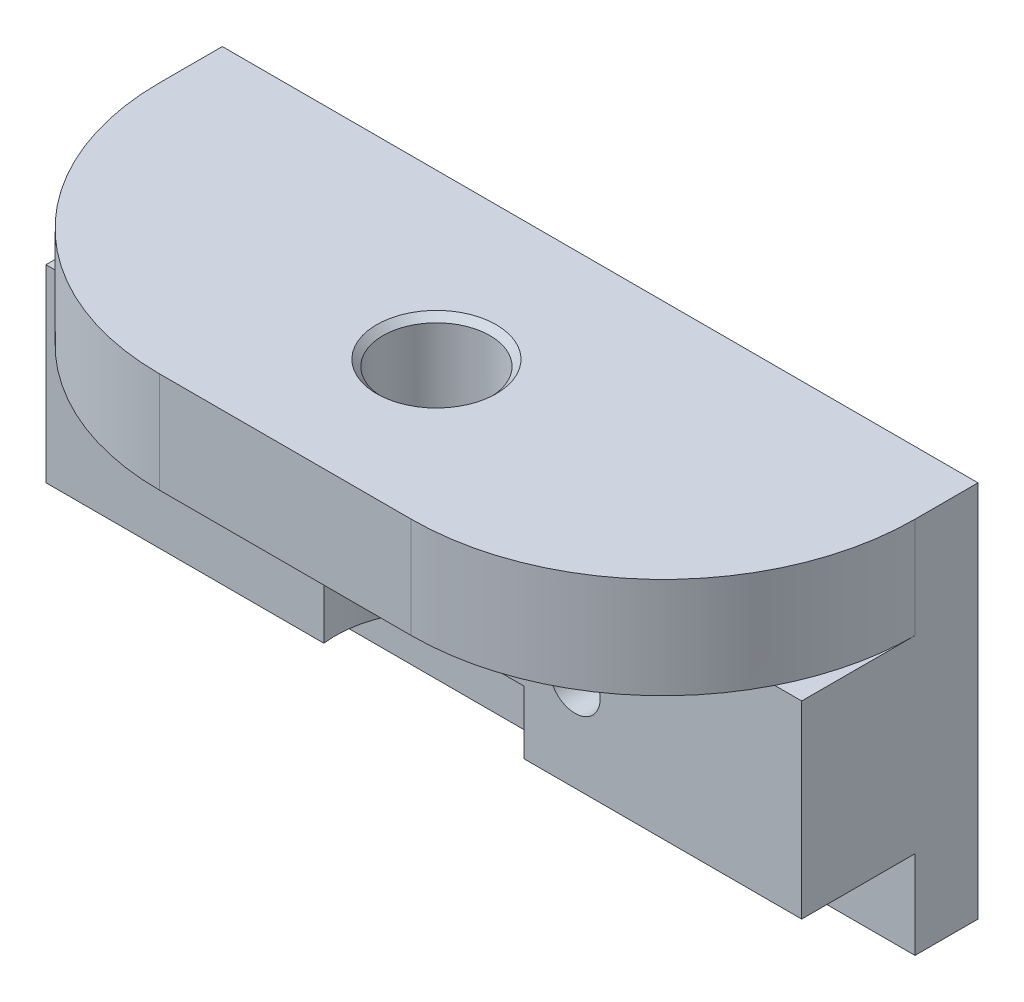
SolidWorks part; units mm, degrees
ref_plane "Piano frontale" through (0, 0, 0) normal (0, 0, 1) x (1, 0, 0)
ref_plane "Piano superiore" through (0, 0, 0) normal (0, 1, 0) x (1, 0, 0)
ref_plane "Piano destro" through (0, 0, 0) normal (1, 0, 0) x (0, 0, -1)
sketch "Schizzo1" plane through (0, 0, 0) normal (0, 0, 1) x (1, 0, 0)
  line L1 (-30, 15) -> (30, 15)
  line L2 (-30, 15) -> (-30, -15)
  line L3 (-30, -15) -> (30, -15)
  line L4 (30, 15) -> (30, -15)
  line L5 (-30, 15) -> (30, -15) construction
  line L6 (-30, -15) -> (30, 15) construction
  point P0 (0, 0)
  dimension "D1" = 60
  dimension "D2" = 30
extrude "Estrusione-Estrusione1" add sketch "Schizzo1" along normal blind 5
sketch "Schizzo2" plane through (0, 0, 5) normal (0, 0, 1) x (1, 0, 0)
  line L0 (-32.3459, -15) -> (49.5432, -15) construction
  line L1 (-32.3459, -8) -> (49.5432, -8) construction
  line L3 (30, -15) -> (30, 15) construction
  line L4 (-30, 15) -> (30, 15)
  line L5 (-30, 15) -> (-30, 7)
  line L6 (-30, 7) -> (30, 7)
  line L7 (30, 15) -> (30, 7)
  dimension "D1" = 7
extrude "Estrusione-Estrusione2" add sketch "Schizzo2" along normal blind 20
sketch "Schizzo3" plane through (0, 15, 0) normal (0, 1, 0) x (1, 0, 0)
  line L0 (0, 7.3603) -> (0, -33.3603) construction
  line L1 (11, 7.3603) -> (11, -33.3603) construction
  line L2 (30, 0) -> (-30, 0) construction
  line L3 (-11, -13) -> (12.2328, -13) construction
  circle A1 centre (0, -13) radius 4.25
  dimension "D1" = 8.5
  dimension "D3" = 13
extrude "Taglio-Estrusione1" cut sketch "Schizzo3" against normal up to surface (8 mm away) up to face at (-7.5, 7, 20)
fillet "Raccordo1" radius 20 2 edges at (30, 11, 25) (-30, 11, 25)
sketch "Schizzo4" plane through (0, 0, 5) normal (0, 0, 1) x (1, 0, 0)
  line L0 (-30, 7) -> (30, 7) construction
  line L1 (-30, 7) -> (30, 7)
  line L2 (-30, -8) -> (30, -8)
  line L3 (-30, -8) -> (-30, 7)
  line L4 (30, -8) -> (30, 7)
  dimension "D1" = 15
extrude "Estrusione-Estrusione3" add sketch "Schizzo4" along normal blind 10
sketch "Schizzo6" plane through (0, -8, 0) normal (0, -1, 0) x (1, 0, 0)
  line L0 (0, 28.7661) -> (0, -12.0233) construction
  line L1 (0, -7.3603) -> (0, 33.3603) construction
  circle A0 centre (0, 13) radius 8
  dimension "D1" = 16
extrude "Taglio-Estrusione2" cut sketch "Schizzo6" against normal blind 15
ref_plane "Piano1" through (-30, 7, 15) normal (0, -1, 0) x (-1, 0, 0)
sketch "Schizzo8" plane through (0, 0, 15) normal (0, 0, 1) x (1, 0, 0)
  line L1 (-30, 1.5) -> (-30, -3)
  line L3 (30, 1.5) -> (30, -3)
  line L4 (-30, 1.5) -> (30, 1.5)
  line L5 (-30, -3) -> (30, -3)
  line L8 (-31.6659, 1.5) -> (35.7067, 1.5) construction
  line L9 (-31.6659, -3) -> (35.7067, -3) construction
  dimension "D3" = 4.5
extrude "Estrusione-Estrusione4" add sketch "Schizzo8" against normal up to surface (10 mm away) up to face at (0, -10.8, 5)
sketch "Schizzo9" plane through (0, -3, 0) normal (0, -1, 0) x (1, 0, 0)
  line L0 (0, 27.458) -> (0, -16.0891) construction
  line L1 (0, -7.3603) -> (0, 33.3603) construction
  circle A0 centre (0, 13) radius 6.3
extrude "Taglio-Estrusione3" cut sketch "Schizzo9" against normal blind 4.5
sketch "Schizzo10" plane through (0, 0, 15) normal (0, 0, 1) x (1, 0, 0)
  line L0 (-31.0418, -0.85) -> (32.2221, -0.85) construction
  line L1 (-10, 7) -> (10, 7) construction
  circle A1 centre (12, -0.85) radius 2
  circle A2 centre (-12, -0.85) radius 2
  point P2 (0, 7)
  point P9 (0, 7)
  dimension "D1" = 12
  dimension "D2" = 12
extrude "Taglio-Estrusione4" cut sketch "Schizzo10" against normal through all
sketch "Schizzo11" plane through (0, 0, 15) normal (0, 0, 1) x (1, 0, 0)
  line L1 (-30, 7) -> (30, 7)
  line L2 (-30, 7) -> (-30, -8)
  line L3 (-30, -8) -> (30, -8)
  line L4 (30, 7) -> (30, -8)
extrude "Taglio-Estrusione5" cut sketch "Schizzo11" against normal blind 1
ref_plane "Piano2" through (0, 0, 30) normal (0, 0, 1) x (1, 0, 0)
chamfer "Smusso1" distance 0.5 angle 45 1 edges at (0, 15, 8.75)
